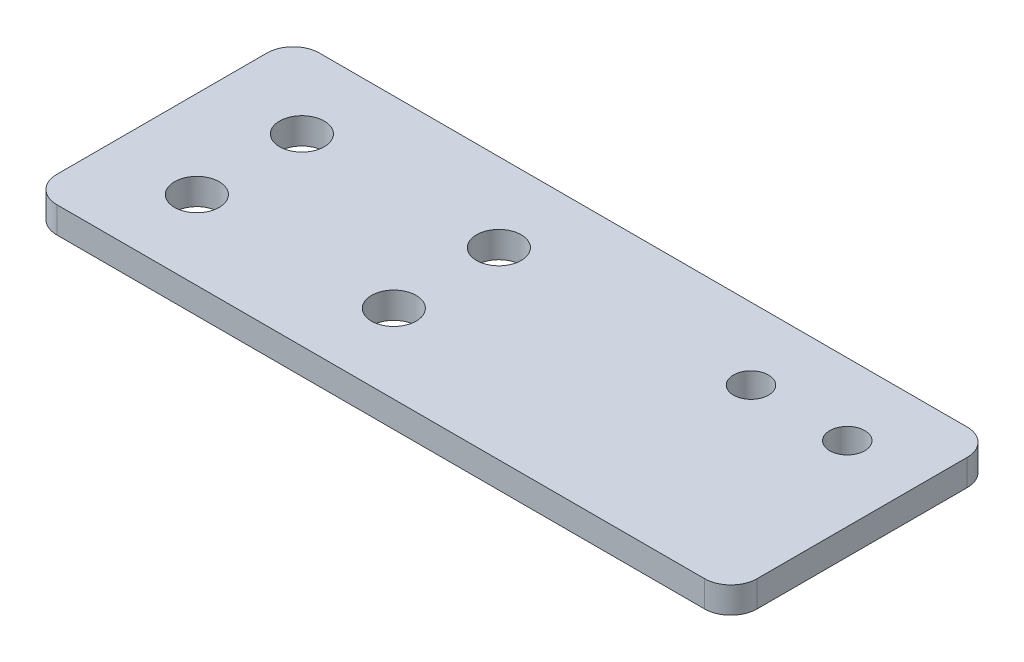
SolidWorks part; units mm, degrees
ref_plane "Front Plane" through (0, 0, 0) normal (0, 0, 1) x (1, 0, 0)
ref_plane "Top Plane" through (0, 0, 0) normal (0, 1, 0) x (1, 0, 0)
ref_plane "Right Plane" through (0, 0, 0) normal (1, 0, 0) x (0, 0, -1)
sketch "Sketch1" plane through (0, 0, 0) normal (0, 1, 0) x (1, 0, 0)
  line L0 (-40, 0) -> (40, 0) construction
  line L1 (-37, 15) -> (37, 15)
  line L2 (-40, 12) -> (-40, -12)
  line L3 (-37, -15) -> (37, -15)
  line L4 (40, 12) -> (40, -12)
  line L5 (-40, 15) -> (40, -15) construction
  line L6 (-40, -15) -> (40, 15) construction
  line L7 (0, 19.1817) -> (0, -19.2392) construction
  line L8 (2.5, 19.1817) -> (2.5, -19.2392) construction
  arc A0 (40, 12) -> (37, 15) centre (37, 12) ccw
  arc A1 (37, -15) -> (40, -12) centre (37, -12) ccw
  arc A2 (-37, -15) -> (-40, -12) centre (-37, -12) cw
  arc A3 (-40, 12) -> (-37, 15) centre (-37, 12) cw
  circle A4 centre (20.5, 6.8) radius 2
  circle A5 centre (31.5, 6.8) radius 2
  circle A6 centre (-30, 6) radius 2.55
  circle A7 centre (-30, -6) radius 2.55
  circle A8 centre (-7.5, 6) radius 2.55
  circle A9 centre (-7.5, -6) radius 2.55
  point P0 (0, 0)
  dimension "D3" = 3
  dimension "D4" = 2
  dimension "D5" = 2
  dimension "D6" = 10
  dimension "D8" = 5.1
  dimension "D7" = 9
  dimension "D9" = 4
  dimension "D10" = 8.2
  dimension "D11" = 12
  dimension "D12" = 11
  dimension "D13" = 8.5
  dimension "D14" = 2
  dimension "D15" = 22.5
  dimension "D16" = 10
  dimension "D1" = 30
  dimension "D2" = 80
extrude "Boss-Extrude2" add sketch "Sketch1" along normal blind 3
